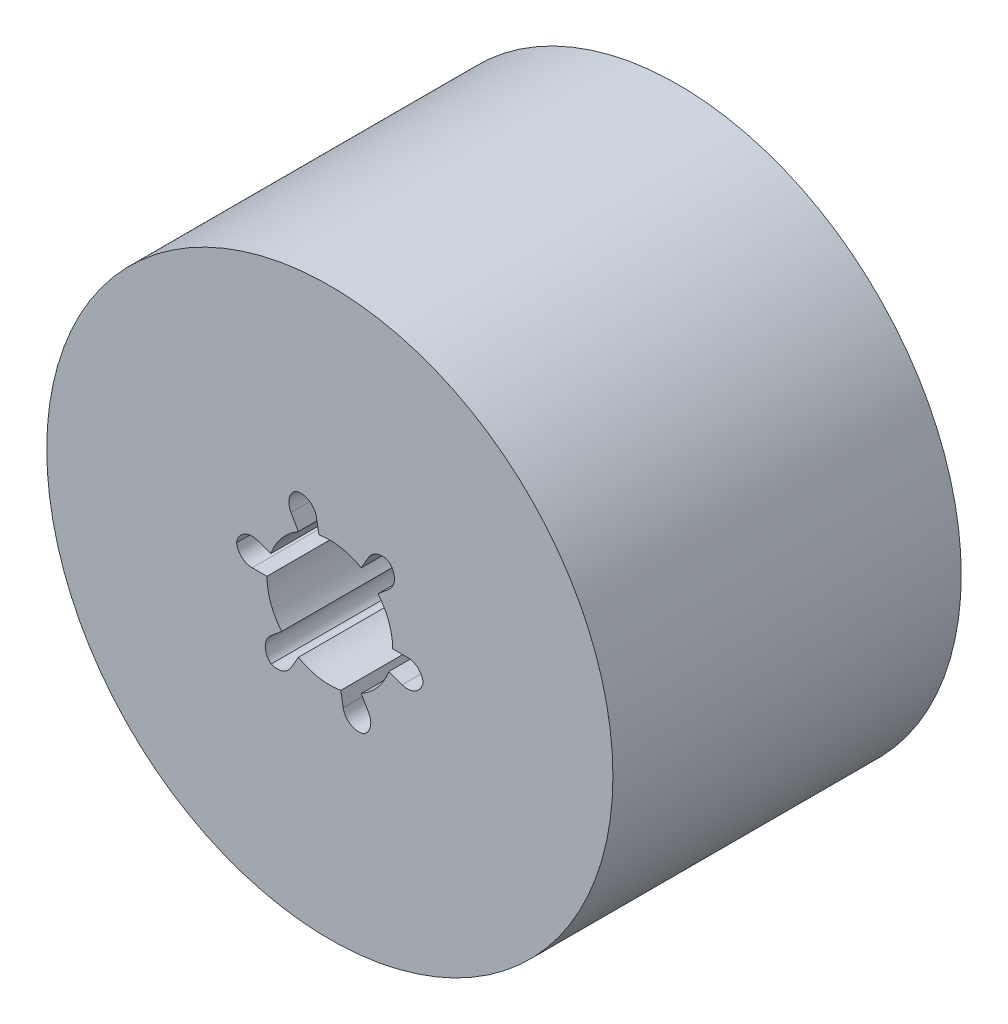
SolidWorks part; units mm, degrees
ref_plane "Front Plane" through (0, 0, 0) normal (0, 0, 1) x (1, 0, 0)
ref_plane "Top Plane" through (0, 0, 0) normal (0, 1, 0) x (1, 0, 0)
ref_plane "Right Plane" through (0, 0, 0) normal (1, 0, 0) x (0, 0, -1)
ref_plane "Plane1" through (0, -43.0601, 0) normal (0, 1, 0) x (1, 0, 0)
sketch "Sketch1" plane through (0, -43.0601, 0) normal (0, 1, 0) x (1, 0, 0)
  line L0 (-62.2567, -35.8) -> (-84.7675, -35.8)
  line L1 (-84.7675, -35.8) -> (-84.7675, -63.5)
  line L2 (-84.7675, -63.5) -> (-62.2567, -63.5)
  line L3 (-62.2567, -63.5) -> (-62.2567, -35.8)
  line L4 (-84.7675, -35.8) -> (-84.7675, -63.5) construction
revolve "Revolve1" add sketch "Sketch1" angle 360 about L4
sketch "Sketch2" plane through (0, 0, 63.5) normal (0, 0, 1) x (1, 0, 0)
  line L0 (-85.6357, -38.1361) -> (-85.8309, -37.0295)
  line L1 (-87.8559, -37.7108) -> (-87.2675, -38.73)
  line L2 (-89.4659, -41.35) -> (-90.5219, -40.9657)
  line L3 (-90.9444, -43.0601) -> (-89.7675, -43.0601)
  line L4 (-88.5977, -46.2741) -> (-89.4585, -46.9964)
  line L5 (-87.8559, -48.4095) -> (-87.2675, -47.3903)
  line L6 (-83.8992, -47.9842) -> (-83.7041, -49.0908)
  line L7 (-81.679, -48.4095) -> (-82.2675, -47.3903)
  line L8 (-80.069, -44.7702) -> (-79.0131, -45.1546)
  line L9 (-78.5906, -43.0601) -> (-79.7675, -43.0601)
  line L10 (-80.9373, -39.8462) -> (-80.0764, -39.1239)
  line L11 (-81.679, -37.7108) -> (-82.2675, -38.73)
  arc A0 (-82.2675, -38.73) -> (-85.6357, -38.1361) centre (-84.7675, -43.0601) ccw
  arc A1 (-85.8309, -37.0295) -> (-87.5207, -36.0838) centre (-87.0619, -37.2465) ccw
  arc A2 (-87.5207, -36.0838) -> (-87.8559, -37.7108) centre (-86.7734, -37.0858) ccw
  arc A3 (-87.2675, -38.73) -> (-89.4659, -41.35) centre (-84.7675, -43.0601) ccw
  arc A4 (-90.5219, -40.9657) -> (-92.1858, -41.9564) centre (-90.9494, -42.1403) ccw
  arc A5 (-92.1858, -41.9564) -> (-90.9444, -43.0601) centre (-90.9444, -41.8101) ccw
  arc A6 (-89.7675, -43.0601) -> (-88.5977, -46.2741) centre (-84.7675, -43.0601) ccw
  arc A7 (-89.4585, -46.9964) -> (-89.4326, -48.9327) centre (-88.655, -47.954) ccw
  arc A8 (-89.4326, -48.9327) -> (-87.8559, -48.4095) centre (-88.9385, -47.7845) ccw
  arc A9 (-87.2675, -47.3903) -> (-83.8992, -47.9842) centre (-84.7675, -43.0601) ccw
  arc A10 (-83.7041, -49.0908) -> (-82.0142, -50.0365) centre (-82.4731, -48.8738) ccw
  arc A11 (-82.0142, -50.0365) -> (-81.679, -48.4095) centre (-82.7616, -49.0345) ccw
  arc A12 (-82.2675, -47.3903) -> (-80.069, -44.7702) centre (-84.7675, -43.0601) ccw
  arc A13 (-79.0131, -45.1546) -> (-77.3492, -44.1639) centre (-78.5855, -43.98) ccw
  arc A14 (-77.3492, -44.1639) -> (-78.5906, -43.0601) centre (-78.5906, -44.3101) ccw
  arc A15 (-79.7675, -43.0601) -> (-80.9373, -39.8462) centre (-84.7675, -43.0601) ccw
  arc A16 (-80.0764, -39.1239) -> (-80.1024, -37.1876) centre (-80.8799, -38.1663) ccw
  arc A17 (-80.1024, -37.1876) -> (-81.679, -37.7108) centre (-80.5965, -38.3358) ccw
extrude "Cut-Extrude1" cut sketch "Sketch2" against normal blind 18.95
hole_wizard "Ø7.5 (7.5) Diameter Hole1" positions "Sketch4" profile "Sketch3" hole size "Ø7.5" standard "ANSI Metric"
sketch "Sketch4" plane through (0, 0, 44.55) normal (0, 0, 1) x (1, 0, 0)
  point P0 (-84.7675, -43.0601)
sketch "Sketch3" plane through (-84.7675, -43.0601, 44.55) normal (1, 0, 0) x (0, -1, 0)
  line L0 (0, 0) -> (0, 3.75)
  line L1 (0, 3.75) -> (3.75, 3.75)
  line L2 (3.75, 3.75) -> (3.75, 0)
  line L5 (3.75, 0) -> (0, 0)
  line L10 (0, 3.75) -> (-3.75, 3.75) construction
  line L11 (0, -6.35) -> (0, 107.95) construction
  dimension "Hole Dia." = 7.5
  dimension "Hole Depth" = 3.75
  dimension "Drill Angle" = 180
